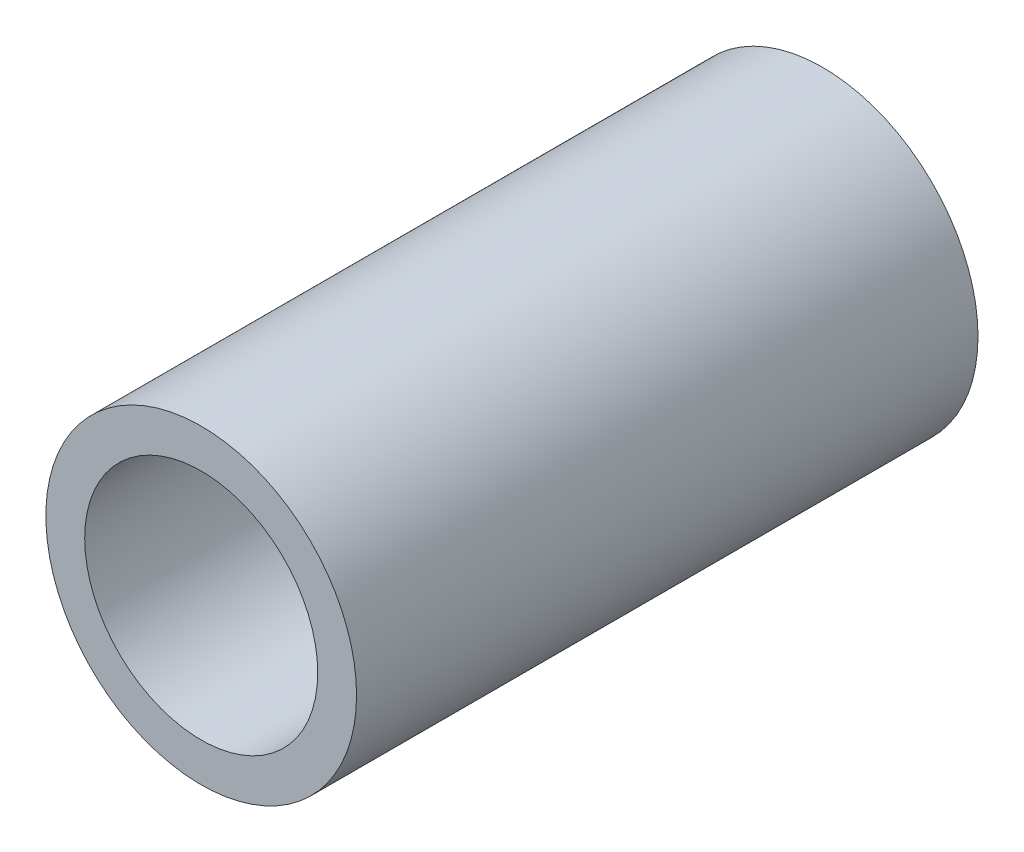
SolidWorks part; units mm, degrees
ref_plane "前视基准面" through (0, 0, 0) normal (0, 0, 1) x (1, 0, 0)
ref_plane "上视基准面" through (0, 0, 0) normal (0, 1, 0) x (1, 0, 0)
ref_plane "右视基准面" through (0, 0, 0) normal (1, 0, 0) x (0, 0, -1)
sketch "草图1" plane through (0, 0, 0) normal (0, 0, 1) x (1, 0, 0)
  circle A0 centre (0, 0) radius 4
  circle A1 centre (0, 0) radius 3
  dimension "D1" = 8
  dimension "D2" = 6
extrude "凸台-拉伸1" add sketch "草图1" along normal blind 16
